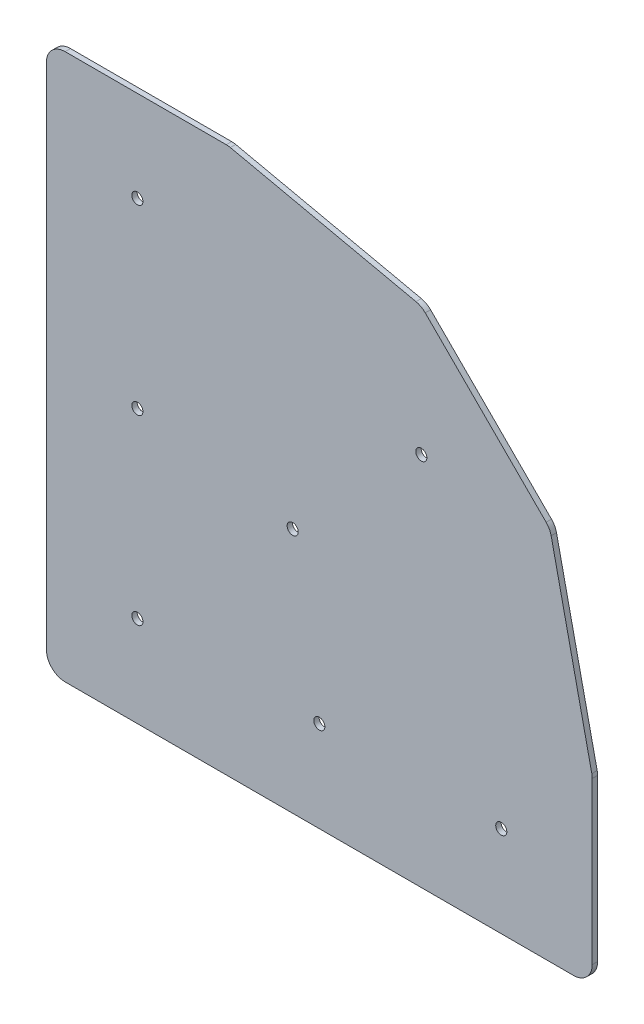
SolidWorks part; units mm, degrees
ref_plane "Front Plane" through (0, 0, 0) normal (0, 0, 1) x (1, 0, 0)
ref_plane "Top Plane" through (0, 0, 0) normal (0, 1, 0) x (1, 0, 0)
ref_plane "Right Plane" through (0, 0, 0) normal (1, 0, 0) x (0, 0, -1)
ref_plane "Plane1" through (0, 0, 0) normal (0, 0, -1) x (-1, 0, 0)
sketch "Sketch1" plane through (0, 0, 0) normal (0, 0, -1) x (-1, 0, 0)
  line L0 (-156.3688, 0) -> (-5.5563, 0)
  line L1 (0, 5.5563) -> (0, 156.3688)
  line L2 (-5.5563, 161.925) -> (-53.3738, 161.925)
  line L3 (-54.5622, 161.7964) -> (-109.6344, 149.7383)
  line L4 (-112.3749, 148.2395) -> (-148.2395, 112.3749)
  line L5 (-149.7383, 109.6344) -> (-161.7964, 54.5622)
  line L6 (-161.925, 53.3738) -> (-161.925, 5.5563)
  circle A0 centre (-26.9875, 134.9375) radius 1.651
  circle A1 centre (-26.9875, 80.9625) radius 1.651
  circle A2 centre (-26.9875, 26.9875) radius 1.651
  circle A3 centre (-134.9375, 26.9875) radius 1.651
  circle A4 centre (-73.058, 73.058) radius 1.651
  circle A5 centre (-111.2241, 111.2241) radius 1.651
  circle A6 centre (-80.9625, 26.9875) radius 1.651
  arc A7 (-161.925, 5.5563) -> (-156.3688, 0) centre (-156.3688, 5.5563) ccw
  arc A8 (-5.5563, 0) -> (0, 5.5563) centre (-5.5563, 5.5563) ccw
  arc A9 (0, 156.3688) -> (-5.5563, 161.925) centre (-5.5563, 156.3688) ccw
  arc A10 (-53.3738, 161.925) -> (-54.5622, 161.7964) centre (-53.3738, 156.3687) ccw
  arc A11 (-109.6344, 149.7383) -> (-112.3749, 148.2395) centre (-108.446, 144.3106) ccw
  arc A12 (-148.2395, 112.3749) -> (-149.7383, 109.6344) centre (-144.3106, 108.446) ccw
  arc A13 (-161.7964, 54.5622) -> (-161.925, 53.3738) centre (-156.3687, 53.3738) ccw
extrude "Boss-Extrude1" add sketch "Sketch1" against normal blind 1.5875
